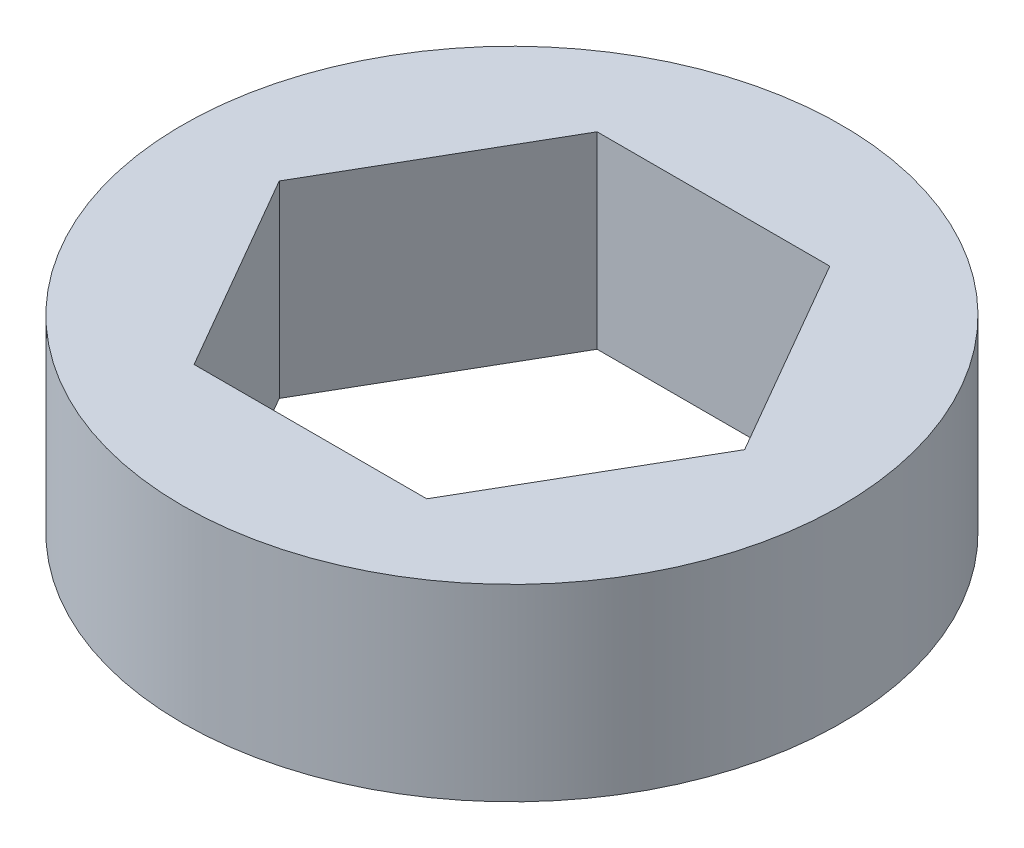
SolidWorks part; units mm, degrees
ref_plane "Front" through (0, 0, 0) normal (0, 0, 1) x (1, 0, 0)
ref_plane "Top" through (0, 0, 0) normal (0, 1, 0) x (1, 0, 0)
ref_plane "Right" through (0, 0, 0) normal (1, 0, 0) x (0, 0, -1)
sketch "Sketch1" plane through (0, 0, 0) normal (0, 1, 0) x (1, 0, 0)
  line L1 (7.8456, 0) -> (3.9228, 6.7945)
  line L2 (3.9228, 6.7945) -> (-3.9228, 6.7945)
  line L3 (-3.9228, 6.7945) -> (-7.8456, 0)
  line L4 (-7.8456, 0) -> (-3.9228, -6.7945)
  line L5 (-3.9228, -6.7945) -> (3.9228, -6.7945)
  line L6 (3.9228, -6.7945) -> (7.8456, 0)
  circle A0 centre (0, 0) radius 6.7945 construction
  circle A1 centre (0, 0) radius 11.1125
  dimension "D1" = 22.225
extrude "Boss-Extrude1" add sketch "Sketch1" along normal blind 6.35
